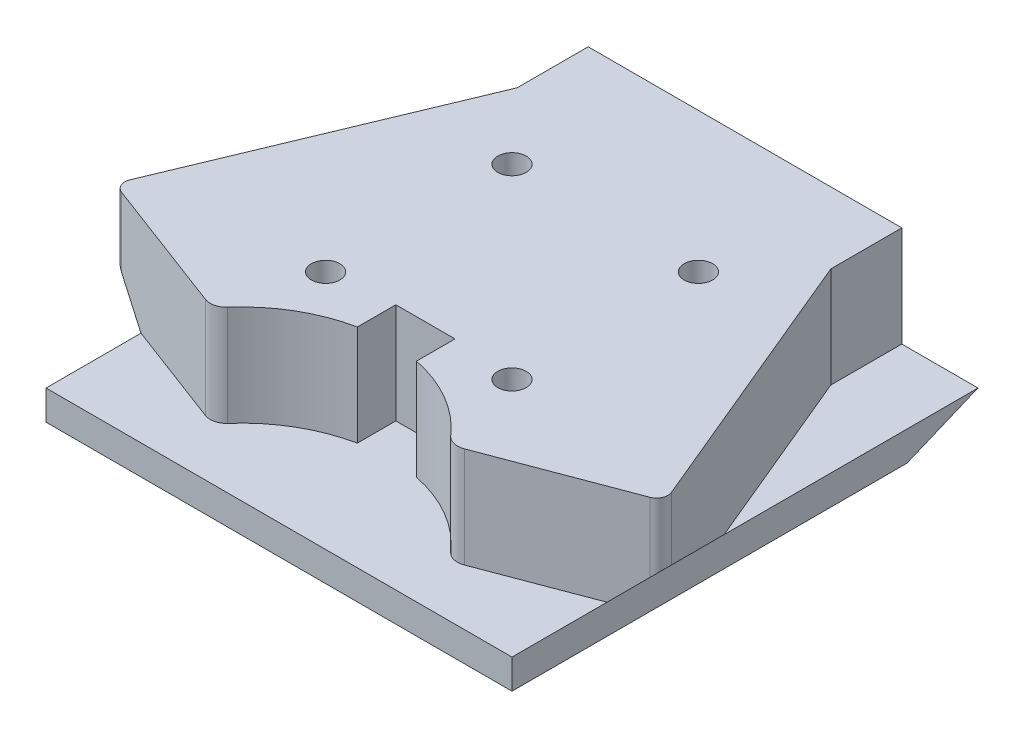
SolidWorks part; units mm, degrees
ref_plane "Front Plane" through (0, 0, 0) normal (0, 0, 1) x (1, 0, 0)
ref_plane "Top Plane" through (0, 0, 0) normal (0, 1, 0) x (1, 0, 0)
ref_plane "Right Plane" through (0, 0, 0) normal (1, 0, 0) x (0, 0, -1)
sketch "Sketch1" plane through (0, 0, 0) normal (0, 1, 0) x (1, 0, 0)
  line L0 (0, 0) -> (33.655, 0)
  line L1 (33.655, 0) -> (33.655, -7.62)
  line L4 (-11.5118, -38.5484) -> (2.9393, -44.0016)
  line L7 (33.655, -7.62) -> (45.8823, -36.9656)
  line L8 (0, 0) -> (0, -7.62)
  line L9 (0, -7.62) -> (-12.2273, -36.9656)
  line L12 (20.0025, -38.1) -> (20.0025, -34.29)
  line L16 (30.7157, -44.0016) -> (45.1668, -38.5484)
  line L17 (20.0025, -34.29) -> (13.6525, -34.29)
  line L18 (13.6525, -34.29) -> (13.6525, -38.1)
  line L20 (13.6525, -38.1) -> (13.6525, -38.4207)
  line L21 (20.0025, -38.1) -> (20.0025, -38.4207)
  arc A0 (4.8483, -43.5579) -> (13.6525, -38.4207) centre (16.8275, -53.975) cw
  arc A1 (-11.5118, -38.5484) -> (-12.2273, -36.9656) centre (-11.0781, -37.3992) cw
  arc A2 (45.1668, -38.5484) -> (45.8823, -36.9656) centre (44.7331, -37.3992) ccw
  arc A3 (2.9393, -44.0016) -> (4.8483, -43.5579) centre (3.5619, -42.3517) ccw
  arc A4 (30.7157, -44.0016) -> (28.8067, -43.5579) centre (30.0931, -42.3517) cw
  arc A5 (20.0025, -38.4207) -> (28.8067, -43.5579) centre (16.8275, -53.975) cw
extrude "Boss-Extrude1" add sketch "Sketch1" along normal blind 10.795
sketch "Sketch2" plane through (0, 0, 0) normal (0, -1, 0) x (1, 0, 0)
  line L0 (16.8275, 0) -> (-8.1725, 0)
  line L1 (33.655, 0) -> (0, 0) construction
  line L2 (-8.1725, 0) -> (-8.1725, 49.9999)
  line L3 (-8.1725, 49.9999) -> (41.8274, 49.9999)
  line L4 (41.8274, 49.9999) -> (41.8274, 0)
  line L5 (41.8274, 0) -> (16.8275, 0)
extrude "Boss-Extrude2" add sketch "Sketch2" along normal blind 3.175
sketch "Sketch3" plane through (-8.1725, 0, 0) normal (-1, 0, 0) x (0, 0, 1)
  line L1 (49.9999, -3.175) -> (0, -3.175) construction
  line L2 (7.62, -3.175) -> (0, 0)
  line L4 (7.62, -3.175) -> (0, -3.175)
  line L5 (0, -3.175) -> (0, 0)
extrude "Cut-Extrude1" cut sketch "Sketch3" against normal through all
sketch "Sketch4" plane through (0, 0, 0) normal (0, 0, -1) x (-1, 0, 0)
  line L8 (-41.8274, 0) -> (-47.9716, 0)
  line L9 (-47.9716, 0) -> (-47.9716, 6.1441)
  line L10 (-41.8274, 0) -> (-47.9716, 6.1441)
  line L11 (8.1725, 0) -> (16.0732, 0)
  line L12 (16.0732, 0) -> (16.0732, 7.9007)
  line L13 (8.1725, 0) -> (16.0732, 7.9007)
extrude "Cut-Extrude3" cut sketch "Sketch4" against normal through all
sketch "Sketch5" plane through (0, -3.175, 0) normal (0, -1, 0) x (1, 0, 0)
  circle A0 centre (6.8275, 35) radius 1.524
  circle A1 centre (26.8275, 35) radius 1.524
  circle A2 centre (6.8275, 14.9999) radius 1.524
  circle A3 centre (26.8275, 14.9999) radius 1.524
extrude "Cut-Extrude4" cut sketch "Sketch5" against normal through all
